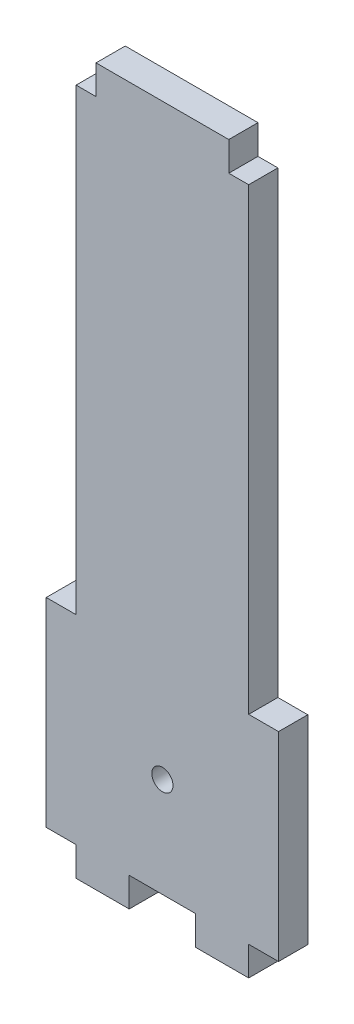
SolidWorks part; units mm, degrees
ref_plane "前视基准面" through (0, 0, 0) normal (0, 0, 1) x (1, 0, 0)
ref_plane "上视基准面" through (0, 0, 0) normal (0, 1, 0) x (1, 0, 0)
ref_plane "右视基准面" through (0, 0, 0) normal (1, 0, 0) x (0, 0, -1)
sketch "草图1" plane through (0, 0, 0) normal (0, 0, 1) x (1, 0, 0)
  line L0 (5, 19.4) -> (5, 15)
  line L1 (5, 19.4) -> (13, 19.4)
  line L2 (5, 15) -> (-5, 15)
  line L3 (13, 19.4) -> (13, 15)
  line L4 (17.5, 15) -> (17.5, -15)
  line L5 (0, -15) -> (0, 15) construction
  line L6 (0, 0) -> (17.5, 0) construction
  line L7 (13, 15) -> (17.5, 15)
  line L8 (-13, 15) -> (-17.5, 15)
  line L9 (-17.5, 15) -> (-17.5, -15)
  line L10 (-13, 19.4) -> (-13, 15)
  line L11 (-5, 19.4) -> (-13, 19.4)
  line L12 (-5, 19.4) -> (-5, 15)
  line L13 (-5, -19.4) -> (-5, -15)
  line L14 (-5, -19.4) -> (-13, -19.4)
  line L15 (-13, -19.4) -> (-13, -15)
  line L16 (-13, -15) -> (-17.5, -15)
  line L17 (13, -15) -> (17.5, -15)
  line L18 (13, -19.4) -> (13, -15)
  line L19 (5, -15) -> (-5, -15)
  line L20 (5, -19.4) -> (13, -19.4)
  line L21 (5, -19.4) -> (5, -15)
  point P0 (0, 0)
  point P21 (-17.5, 0)
  dimension "D1" = 35
  dimension "D2" = 30
  dimension "D3" = 4.4
  dimension "D4" = 8
  dimension "D5" = 10
extrude "凸台-拉伸1" add sketch "草图1" along normal blind 4.4
sketch "草图2" plane through (0, 0, 4.4) normal (0, 0, 1) x (1, 0, 0)
  line L0 (5, 15) -> (-5, 15) construction
  circle A0 centre (0, 0) radius 1.6
  dimension "D1" = 3.2
  dimension "D2" = 15
extrude "切除-拉伸1" cut sketch "草图2" against normal blind 10 contours A0
sketch "草图3" plane through (0, 0, 4.4) normal (0, 0, 1) x (1, 0, 0)
  line L0 (10, 88.5) -> (10, 84.1)
  line L1 (-13, 15) -> (13, 15)
  line L2 (-13, 15) -> (-13, 84.1)
  line L3 (-10, 88.5) -> (10, 88.5)
  line L4 (13, 15) -> (13, 84.1)
  line L5 (10, 84.1) -> (13, 84.1)
  line L6 (0, 13.5) -> (0, 93.3781) construction
  line L7 (-10, 84.1) -> (-13, 84.1)
  line L8 (-10, 88.5) -> (-10, 84.1)
  dimension "D1" = 73.5
  dimension "D2" = 20
  dimension "D3" = 4.4
extrude "凸台-拉伸2" add sketch "草图3" against normal up to surface (4.4 mm away) up to face at (-1.6, 0, 0)
